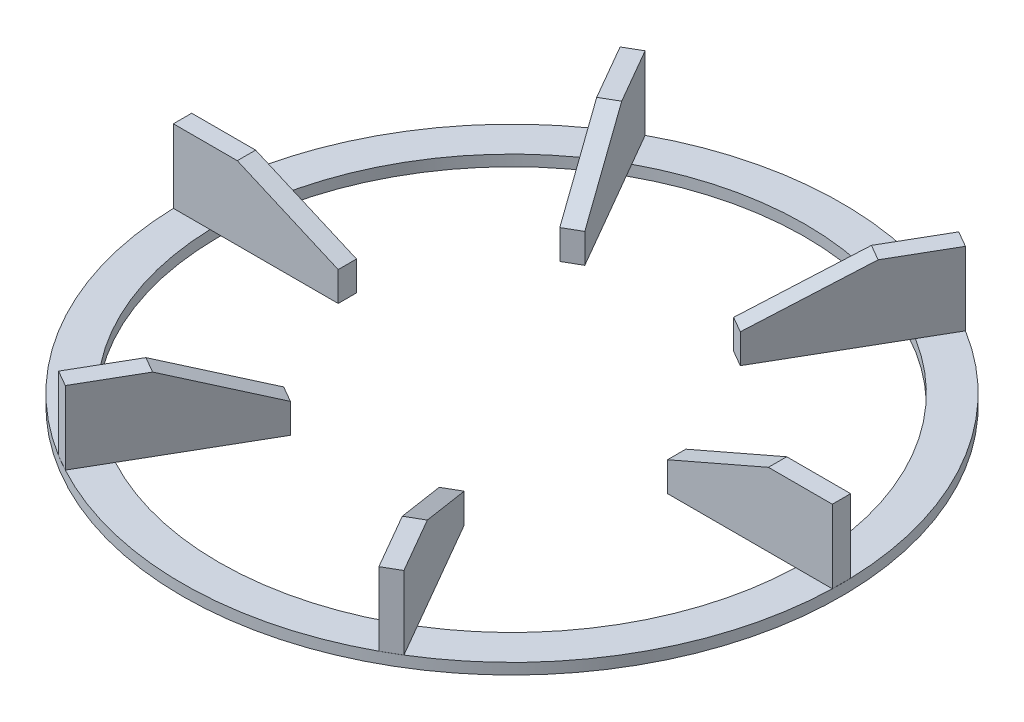
SolidWorks part; units mm, degrees
material "AISI 316 Stainless Steel Sheet (SS)"
ref_plane "Front Plane" through (0, 0, 0) normal (0, 0, 1) x (1, 0, 0)
ref_plane "Top Plane" through (0, 0, 0) normal (0, 1, 0) x (1, 0, 0)
ref_plane "Right Plane" through (0, 0, 0) normal (1, 0, 0) x (0, 0, -1)
sketch "Sketch1" plane through (0, 0, 0) normal (0, 1, 0) x (1, 0, 0)
  circle A0 centre (0, 0) radius 90
extrude "Extrude-Thin1" add sketch "Sketch1" along normal blind 3 thin thin type one direction reverse wall 10
sketch "Sketch2" plane through (0, 3, 0) normal (0, 1, 0) x (1, 0, 0)
  line L0 (0, 0) -> (44.9653, 0) construction
  line L1 (89.9653, -2.5) -> (44.9653, -2.5)
  line L2 (89.9653, -2.5) -> (89.9653, 2.5)
  line L3 (89.9653, 2.5) -> (44.9653, 2.5)
  line L4 (44.9653, -2.5) -> (44.9653, 2.5)
  circle A2 centre (0, 0) radius 90 construction
extrude "Boss-Extrude1" add sketch "Sketch2" along normal blind 20
sketch "Sketch3" plane through (0, 0, 2.5) normal (0, 0, 1) x (1, 0, 0)
  line L0 (44.9653, 11.0227) -> (72.5105, 23)
  line L1 (44.9653, 23) -> (44.9653, 3) construction
  line L2 (44.9653, 23) -> (89.9653, 23) construction
  line L3 (72.5105, 23) -> (44.9653, 23)
  line L4 (44.9653, 23) -> (44.9653, 11.0227)
extrude "Cut-Extrude1" cut sketch "Sketch3" against normal blind 5
pattern_circular "CirPattern1" count 6 over 360 about axis through (0, 0, 0) along (0, 1, 0) of "Boss-Extrude1", "Cut-Extrude1"
scale "Scale1" scale about centroid uniform scaling yes scale factor 1.25
